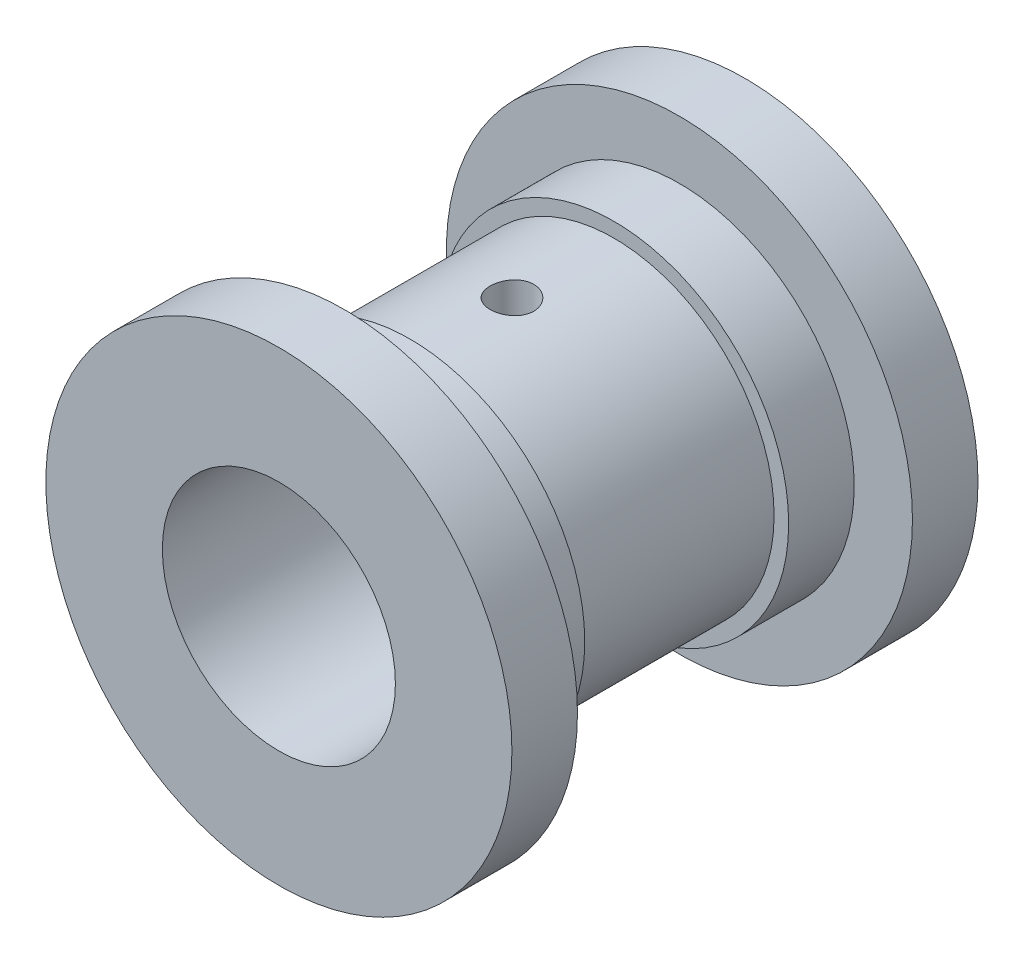
SolidWorks part; units mm, degrees
ref_plane "Front Plane" through (0, 0, 0) normal (0, 0, 1) x (1, 0, 0)
ref_plane "Top Plane" through (0, 0, 0) normal (0, 1, 0) x (1, 0, 0)
ref_plane "Right Plane" through (0, 0, 0) normal (1, 0, 0) x (0, 0, -1)
sketch "Sketch1" plane through (0, 0, 0) normal (0, 0, 1) x (1, 0, 0)
  circle A0 centre (0, 0) radius 22
  dimension "D1" = 44
extrude "Boss-Extrude1" add sketch "Sketch1" along normal mid plane 28
sketch "Sketch2" plane through (0, 0, 14) normal (0, 0, 1) x (1, 0, 0)
  circle A0 centre (0, 0) radius 24
  dimension "D1" = 48
extrude "Boss-Extrude2" add sketch "Sketch2" along normal blind 9
mirror "Mirror1" about plane through (0, 0, 0) normal (0, 0, 1) of "Boss-Extrude2"
sketch "Sketch3" plane through (0, 0, 23) normal (0, 0, 1) x (1, 0, 0)
  circle A0 centre (0, 0) radius 32
  dimension "D1" = 64
extrude "Boss-Extrude3" add sketch "Sketch3" along normal blind 9
mirror "Mirror2" about plane through (0, 0, 0) normal (0, 0, 1) of "Boss-Extrude3"
sketch "Sketch4" plane through (0, 0, 32) normal (0, 0, 1) x (1, 0, 0)
  circle A0 centre (0, 0) radius 16
  dimension "D1" = 32
sketch "Sketch5" plane through (0, 0, 0) normal (0, 1, 0) x (1, 0, 0)
  circle A0 centre (0, 0) radius 4
  dimension "D1" = 8
extrude "Boss-Extrude4" add sketch "Sketch5" against normal blind 30
extrude "Cut-Extrude2" cut sketch "Sketch4" against normal up to next contours A0
sketch "Sketch6" plane through (0, -30, 0) normal (0, -1, 0) x (1, 0, 0)
  circle A0 centre (0, 0) radius 3
  dimension "D1" = 6
extrude "Cut-Extrude3" cut sketch "Sketch6" against normal through all
